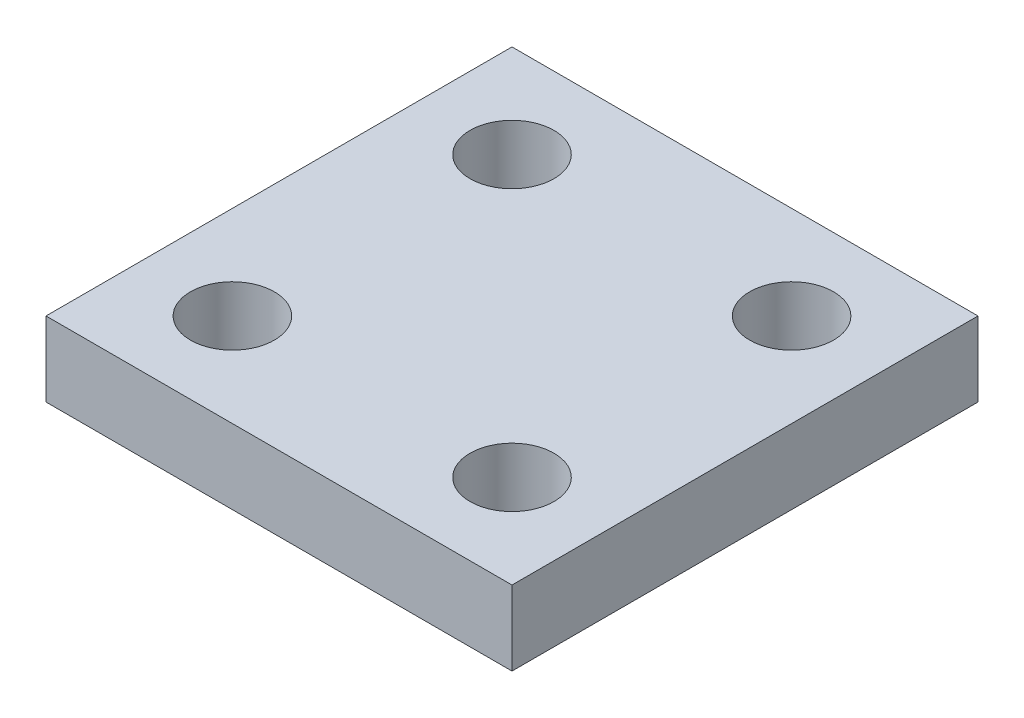
SolidWorks part; units mm, degrees
ref_plane "Front Plane" through (0, 0, 0) normal (0, 0, 1) x (1, 0, 0)
ref_plane "Top Plane" through (0, 0, 0) normal (0, 1, 0) x (1, 0, 0)
ref_plane "Right Plane" through (0, 0, 0) normal (1, 0, 0) x (0, 0, -1)
sketch "草圖1" plane through (0, 0, 0) normal (0, 1, 0) x (1, 0, 0)
  line L1 (-12.5, 12.5) -> (12.5, 12.5)
  line L2 (-12.5, 12.5) -> (-12.5, -12.5)
  line L3 (-12.5, -12.5) -> (12.5, -12.5)
  line L4 (12.5, 12.5) -> (12.5, -12.5)
  line L5 (-12.5, 12.5) -> (12.5, -12.5) construction
  line L6 (-12.5, -12.5) -> (12.5, 12.5) construction
  line L7 (-7.5, 7.5) -> (7.5, 7.5) construction
  line L8 (-7.5, 7.5) -> (-7.5, -7.5) construction
  line L9 (-7.5, -7.5) -> (7.5, -7.5) construction
  line L10 (7.5, 7.5) -> (7.5, -7.5) construction
  line L11 (-7.5, 7.5) -> (7.5, -7.5) construction
  line L12 (-7.5, -7.5) -> (7.5, 7.5) construction
  circle A0 centre (-7.5, 7.5) radius 2.25
  circle A1 centre (7.5, -7.5) radius 2.25
  circle A2 centre (-7.5, -7.5) radius 2.25
  circle A3 centre (7.5, 7.5) radius 2.25
  point P0 (0, 0)
  point P8 (0, 0)
  dimension "D5" = 4.5
  dimension "D1" = 25
  dimension "D2" = 25
  dimension "15" = 15
  dimension "D4" = 15
extrude "填料-伸長1" add sketch "草圖1" along normal blind 4
